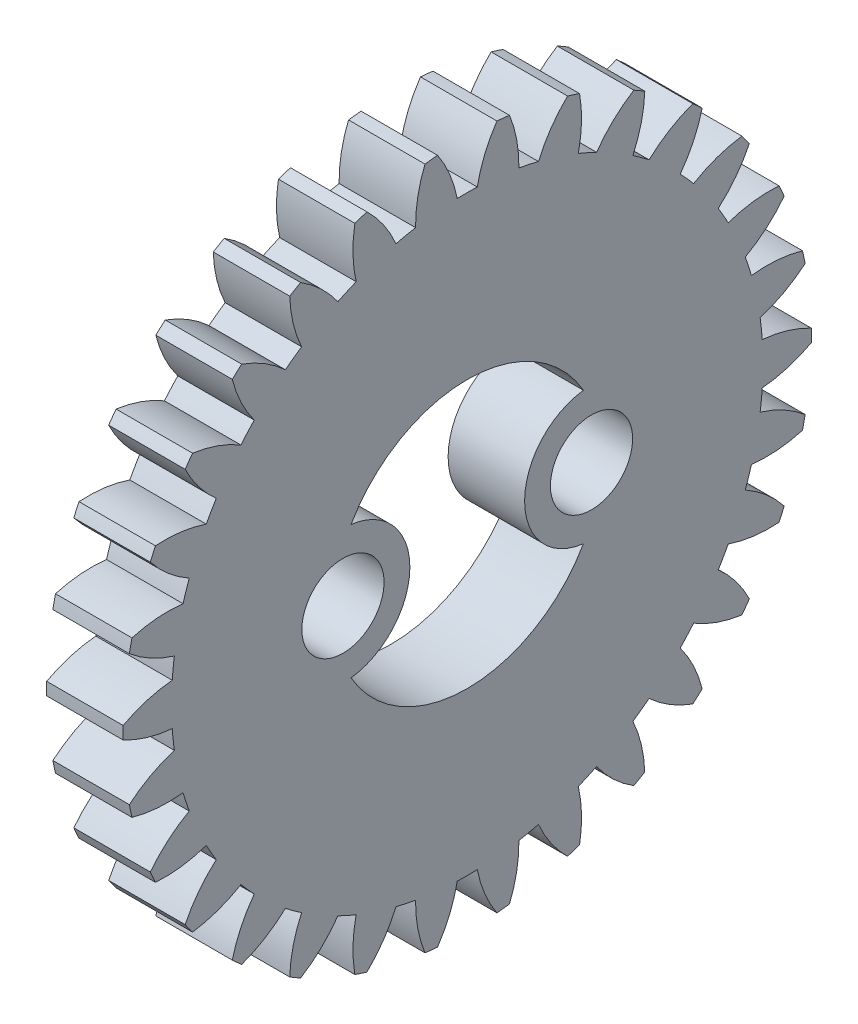
SolidWorks part; units mm, degrees
material "PLA"
ref_plane "Plane1" through (0, 0, 0) normal (0, 0, 1) x (1, 0, 0)
ref_plane "Plane2" through (0, 0, 0) normal (0, 1, 0) x (1, 0, 0)
ref_plane "Plane3" through (0, 0, 0) normal (1, 0, 0) x (0, 0, -1)
other "Configuration Table"
sketch "HoldingSke" plane through (0, 0, 0) normal (0, 1, 0) x (1, 0, 0)
  line L0 (0, 0) -> (0.7698, -0.4444)
  line L1 (-15, 0) -> (100, 0) construction
  line L2 (0, 0) -> (-2.1039, 2.3779)
  line L3 (0, 0) -> (-11.863, 4.5341)
  line L4 (0, 0) -> (7.479, 4.318)
  line L5 (0, 0) -> (-46.8476, -17.4728)
  line L6 (0, 0) -> (-3.3159, -2.2372)
  line L7 (-2.1039, 2.3779) -> (8.6586, 51.2059)
  line L8 (-76.2, 54.61) -> (-75.7, 54.61)
  line L9 (-71.009, 38.7566) -> (-53.1078, 45.2721)
  line L10 (-76.2, 71.12) -> (104.1128, 71.12)
  line L11 (0, 0) -> (-4, 0)
  line L12 (-76.2, 101.6) -> (-76.158, 101.6)
  line L13 (24.9733, 27.94) -> (52.9518, 28.4284)
  line L14 (24.9733, 27.94) -> (24.9743, 27.94)
  line L15 (24.9733, 27.94) -> (100.4006, 29.5858)
  line L16 (-63.627, -1.125) -> (-12.827, -1.125)
  circle A0 centre (0, 0) radius 1.5
  circle A1 centre (0, 0) radius 15.4677
  circle A2 centre (0, 0) radius 37.5
  circle A3 centre (0, 0) radius 1.5
  dimension "MHD" = 30.9355
  dimension "Hub_dia" = 75
  dimension "Bore" = 3
  dimension "MBD" = 3
  dimension "Num_teeth" = 30
  dimension "Pitch" = 0.8889
  dimension "Overall_len" = 50
  dimension "Show_teeth" = 30
  dimension "Thickness" = 4
  dimension "OAL" = 50.0001
  dimension "T_dim" = 0.5
  dimension "Ap" = 20
  dimension "H" = 19.05
  dimension "Pitch_radius" = 180.3128
  dimension "Width" = 4
  dimension "Backlash" = 0.042
  dimension "Addendum_fac" = 1
  dimension "Dedendum_fac" = 1.25
  dimension "Clearance_fac" = 0.25
  dimension "Dedendum_add" = 0.001
  dimension "Module" = 1.125
sketch "BasProSke" plane through (0, 0, 0) normal (0, 1, 0) x (1, 0, 0)
  line L0 (-10, 0) -> (60, 0) construction
  line L1 (0, 0) -> (0, 18)
  line L2 (0, 0) -> (4, 0)
  line L3 (4, 0) -> (4, 18)
  line L4 (4, 18) -> (0, 18)
  dimension "Thickness" = 4
  dimension "Diameter" = 36
revolve "Base-Revolve" add sketch "BasProSke" angle 360 about L0
sketch "TooCutSke" plane through (0, 0, 0) normal (1, 0, 0) x (0, 0, -1)
  line L1 (0, 0) -> (0, 107) construction
  line L2 (0, 0) -> (-0.9567, 16.8479) construction
  line L3 (0, 0) -> (-3.5238, 33.5265) construction
  line L4 (-0.9567, 16.8479) -> (-1.7619, 16.7632) construction
  arc A0 (0.5235, 15.4589) -> (-0.5235, 15.4589) centre (0, 0) ccw
  arc A1 (1.5687, 17.957) -> (-1.5687, 17.957) centre (0, 0) ccw
  circle A2 centre (0, 0) radius 16.875 construction
  circle A3 centre (0, 0) radius 15.8573 construction
  arc A4 (-0.5235, 15.4589) -> (-1.5687, 17.957) centre (-7.1465, 14.1556) ccw
  arc A5 (1.5687, 17.957) -> (0.5235, 15.4589) centre (7.1465, 14.1556) ccw
  dimension "Root_dia" = 30.9355
  dimension "Overcut_dia" = 36.0508
  dimension "Pitch_dia" = 33.75
  dimension "Base_dia" = 31.7146
  dimension "Flank_rad" = 6.75
  dimension "Half_ang" = 6
  dimension "Half_CT" = 0.8097
extrude "ToothCut" cut sketch "TooCutSke" along normal through all
fillet "Breaks" [suppressed] radius 0.0225
fillet "RootFillets" [suppressed] radius 0.2823
pattern_circular "TeethCuts" count 30 every 12 about axis through (-10, 0, 0) along (1, 0, 0) of "ToothCut", "RootFillets", "Breaks"
sketch "HubNeaOneSke" plane through (0, 0, 0) normal (-1, 0, 0) x (0, 0, 1)
  circle A0 centre (0, 0) radius 15.4677
  dimension "Diameter" = 30.9355
extrude "HubNearOne" [suppressed] add sketch "HubNeaOneSke" along normal blind 46.0001
sketch "HubNeaBotSke" plane through (0, 0, 0) normal (-1, 0, 0) x (0, 0, 1)
  circle A0 centre (0, 0) radius 15.4677
  dimension "Diameter" = 30.9355
extrude "HubNearBoth" [suppressed] add sketch "HubNeaBotSke" along normal blind 23
ref_plane "FarPln" through (4, 0, 0) normal (1, 0, 0) x (0, 0, -1)
sketch "HubFarSke" plane through (4, 0, 0) normal (1, 0, 0) x (0, 0, -1)
  circle A0 centre (0, 0) radius 15.4677
  dimension "Diameter" = 30.9355
extrude "HubFar" [suppressed] add sketch "HubFarSke" along normal blind 23
sketch "BorSke" plane through (0, 0, 0) normal (1, 0, 0) x (0, 0, -1)
  circle A0 centre (0, 0) radius 7
  dimension "Diameter" = 14
extrude "Bore" cut sketch "BorSke" along normal mid plane 100.0001
sketch "KeySke" plane through (0, 0, 0) normal (1, 0, 0) x (0, 0, -1)
  line L0 (-0.6, 0) -> (-0.6, 2)
  line L1 (-0.6, 2) -> (0.6, 2)
  line L2 (0.6, 2) -> (0.6, 0)
  line L3 (0, 0) -> (0, 34) construction
  line L4 (-0.6, 0) -> (0.6, 0)
  dimension "Offset" = 2
  dimension "Width" = 1.2
extrude "Keyway" [suppressed] cut sketch "KeySke" along normal mid plane 100.0001
pattern_circular "Keyway2" [suppressed] count 2 every 90 about axis through (-10, 0, 0) along (1, 0, 0)
sketch "Sketch2" plane through (0, 0, 0) normal (-1, 0, 0) x (0, 0, 1)
  line L0 (-6.5, 0) -> (6.5, 0) construction
  circle A0 centre (-6.5, 0) radius 3.5
  circle A1 centre (6.5, 0) radius 3.5
  dimension "D1" = 7
  dimension "D2" = 13
extrude "Boss-Extrude1" add sketch "Sketch2" against normal up to surface (4 mm away) up to face at (4, 0, 7)
hole_wizard "M4 Clearance Hole1" positions "Sketch3" profile "Sketch4" hole size "M4" standard "ANSI Metric" end condition up to next
sketch "Sketch3" plane through (0, 0, 0) normal (-1, 0, 0) x (0, 0, 1)
  point P0 (-6.5, 0)
  point P3 (6.5, 0)
sketch "Sketch4" plane through (0, 0, -6.5) normal (0, 1, 0) x (0, 0, 1)
  line L0 (0, 0) -> (0, 4)
  line L1 (0, 4) -> (2.15, 4)
  line L2 (2.15, 4) -> (2.15, 0)
  line L5 (2.15, 0) -> (0, 0)
  line L11 (0, -6.35) -> (0, 107.95) construction
  dimension "Thru Hole Dia." = 4.3
  dimension "Thru Hole Depth" = 4
equation "' \"Module@HoldingSke\" = 6.35"
equation "' \"Num_teeth@HoldingSke\" = 12"
equation "' \"Ap@HoldingSke\" =  20"
equation "' \"Ap@HoldingSke\" = 20"
equation "' \"Width@HoldingSke\" = 0.5 * 25.4"
equation "' \"Hub_dia@HoldingSke\"= 1 * 25.4"
equation "' \"Hub_dia@HoldingSke\" = 1 * 25.4"
equation "' \"Overall_len@HoldingSke\" = 1.0 * 25.4"
equation "' \"Bore@HoldingSke\" = 0.75 * 25.4"
equation "' \"T_dim@HoldingSke\" = 0.1 * 25.4"
equation "' \"Width@KeySke\" = 0.25 * 25.4"
equation "' \"Show_teeth@HoldingSke\" = 13"
equation "' \"Backlash@HoldingSke\" = 0.009 * 25.4"
equation "' \"Addendum_fac@HoldingSke\" = 1.0"
equation "' \"Dedendum_fac@HoldingSke\" = 1.25"
equation "' \"Dedendum_add@HoldingSke\" = 0.00005 * 25.4"
equation "' \"Clearance_fac@HoldingSke\" = 0.25"
equation "\"Pitch@HoldingSke\" = 1 / \"Module@HoldingSke\""
equation "\"Overcut_dia@TooCutSke\" = (\"Num_teeth@HoldingSke\" + 2 * \"Addendum_fac@HoldingSke\") / \"Pitch@HoldingSke\" + 0.002 * 25.4"
equation "\"Pitch_dia@TooCutSke\" = \"Num_teeth@HoldingSke\" / \"Pitch@HoldingSke\""
equation "\"Base_dia@TooCutSke\" = \"Num_teeth@HoldingSke\" / \"Pitch@HoldingSke\" * cos((\"Ap@HoldingSke\"  * 3.14159265 / 180))"
equation "\"Root_dia@TooCutSke\" = (\"Num_teeth@HoldingSke\" + 2) / \"Pitch@HoldingSke\" - 2 * (\"Addendum_fac@HoldingSke\" + \"Dedendum_fac@HoldingSke\") / \"Pitch@HoldingSke\" - \"Dedendum_add@HoldingSke\" * 2"
equation "\"Half_ang@TooCutSke\" = 180 / \"Num_teeth@HoldingSke\""
equation "\"Half_CT@TooCutSke\" = \"Num_teeth@HoldingSke\" / \"Pitch@HoldingSke\" * sin((3.14159265 / 2 / \"Num_teeth@HoldingSke\")) / 2 - 7 * \"Backlash@HoldingSke\" / 4"
equation "\"Flank_rad@TooCutSke\" = \"Num_teeth@HoldingSke\" / \"Pitch@HoldingSke\" / 5"
equation "\"Radius@RootFillets\" = \"Clearance_fac@HoldingSke\" / \"Pitch@HoldingSke\" + \"Dedendum_add@HoldingSke\""
equation "\"Break_rad@Breaks\" = 0.02 / \"Pitch@HoldingSke\""
equation "\"Thickness@HoldingSke\" = \"Width@HoldingSke\""
equation "\"OAL@HoldingSke\" = \"Thickness@HoldingSke\""
equation "\"MHD@HoldingSke\" = (\"Num_teeth@HoldingSke\" + 2) / \"Pitch@HoldingSke\" - 2 * (\"Addendum_fac@HoldingSke\" + \"Dedendum_fac@HoldingSke\")  / \"Pitch@HoldingSke\" - \"Dedendum_add@HoldingSke\" * 2"
equation "\"MBD@HoldingSke\" = (\"Num_teeth@HoldingSke\" + 2) / \"Pitch@HoldingSke\" - 2 * (\"Addendum_fac@HoldingSke\" + \"Dedendum_fac@HoldingSke\")  / \"Pitch@HoldingSke\" - \"Dedendum_add@HoldingSke\" * 2 - 0.002 * 25.4"
equation "\"MHD@HoldingSke\" = ((sgn( \"MHD@HoldingSke\" - \"Hub_dia@HoldingSke\" )-1)*( \"MHD@HoldingSke\" - \"Hub_dia@HoldingSke\" ))/-2+ \"Hub_dia@HoldingSke\""
equation "\"MBD@HoldingSke\" = ((sgn( \"MBD@HoldingSke\" - \"Bore@HoldingSke\" )-1)*( \"MBD@HoldingSke\" - \"Bore@HoldingSke\" ))/-2+ \"Bore@HoldingSke\""
equation "\"OAL@HoldingSke\" = ((sgn( \"OAL@HoldingSke\" - \"Overall_len@HoldingSke\" )+1)*( \"OAL@HoldingSke\" - \"Overall_len@HoldingSke\" ))/2 + \"Overall_len@HoldingSke\" + 0.000002 * 25.4"
equation "\"Num_teeth@TeethCuts\" = int( \"Show_teeth@HoldingSke\" ) + 1"
equation "\"Num_teeth@TeethCuts\" = ((sgn( \"Num_teeth@TeethCuts\" - \"Num_teeth@HoldingSke\" )-1)*( \"Num_teeth@TeethCuts\" - \"Num_teeth@HoldingSke\" ))/-2+ \"Num_teeth@HoldingSke\""
equation "\"Num_teeth@TeethCuts\" = ((sgn( \"Num_teeth@TeethCuts\" - 2.0)+1)*( \"Num_teeth@TeethCuts\" - 2.0))/2 +2.0"
equation "\"Angle@TeethCuts\" = 360.0 / \"Num_teeth@HoldingSke\""
equation "\"Diameter@BasProSke\" = (\"Num_teeth@HoldingSke\" + 2 * \"Addendum_fac@HoldingSke\") / \"Pitch@HoldingSke\""
equation "\"Thickness@BasProSke\"  = \"Thickness@HoldingSke\""
equation "' \"Fillet_rad@BasProSke\" =  \"Thickness@HoldingSke\" * 0.05"
equation "' \"Fillet_rad@BasProSke\" = \"Thickness@HoldingSke\" * 0.05"
equation "\"MHD@HoldingSke\" = ((sgn( \"MHD@HoldingSke\" - \"Root_dia@TooCutSke\" )-1)*( \"MHD@HoldingSke\" - \"Root_dia@TooCutSke\" ))/-2+ \"Root_dia@TooCutSke\""
equation "\"Diameter@HubNeaOneSke\" = \"MHD@HoldingSke\""
equation "\"Length@HubNearOne\" = \"OAL@HoldingSke\" - \"Thickness@BasProSke\""
equation "\"Diameter@HubNeaBotSke\" = \"MHD@HoldingSke\""
equation "\"Length@HubNearBoth\" = ( \"OAL@HoldingSke\" - \"Thickness@BasProSke\" ) / 2.0"
equation "\"Thickness@FarPln\" = \"Thickness@BasProSke\""
equation "\"Diameter@HubFarSke\" = \"MHD@HoldingSke\""
equation "\"Length@HubFar\" = ( \"OAL@HoldingSke\" - \"Thickness@BasProSke\" ) / 2.0"
equation "\"D1@Bore\" = \"OAL@HoldingSke\" * 2.0"
equation "\"D1@Keyway\" = \"OAL@HoldingSke\" * 2.0"
equation "\"Offset@KeySke\" = \"T_dim@HoldingSke\" + \"MBD@HoldingSke\" / 2.0"
